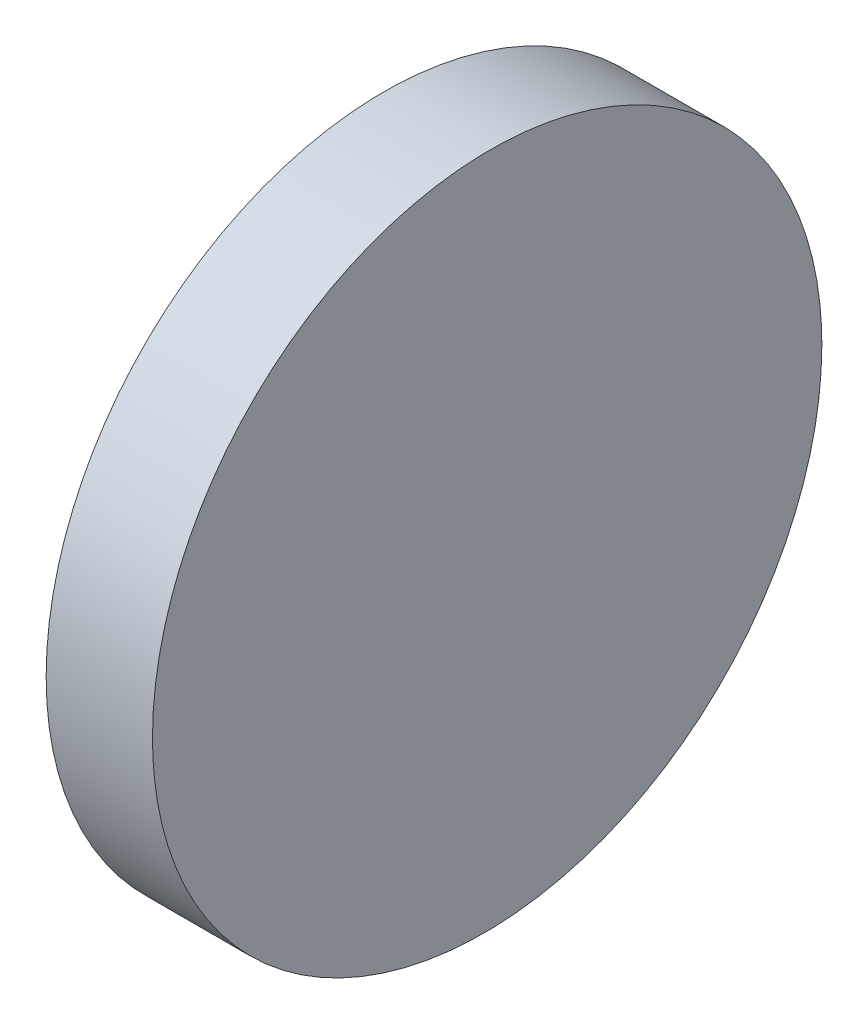
SolidWorks part; units mm, degrees
ref_plane "前视基准面" through (0, 0, 0) normal (0, 0, 1) x (1, 0, 0)
ref_plane "上视基准面" through (0, 0, 0) normal (0, 1, 0) x (1, 0, 0)
ref_plane "右视基准面" through (0, 0, 0) normal (1, 0, 0) x (0, 0, -1)
sketch "草图1" plane through (0, 0, 0) normal (0, 1, 0) x (1, 0, 0)
  line L0 (-12.1202, 0) -> (19.0875, 0) construction
  line L1 (0, 25.4) -> (0, -25.4)
  line L2 (0, -25.4) -> (8, -25.4)
  line L3 (8, -25.4) -> (7.5567, 25.4)
  line L4 (0, 25.4) -> (7.5567, 25.4)
  point P5 (0, 0)
  dimension "D1" = 8
  dimension "D2" = 50.8
  dimension "D3" = 0.5
extrude "凸台-拉伸1" add sketch "草图1" along normal blind 50.8
sketch "草图5" plane through (0, 0, 0) normal (-1, 0, 0) x (0, 0, 1)
  line L0 (0, 0) -> (0, 50.8) construction
  line L1 (-25.4, 50.8) -> (25.4, 50.8) construction
  line L2 (0, 50.8) -> (0.9302, 12.292) construction
  line L3 (-25.4, 25.4) -> (25.4, 25.4) construction
  line L4 (-25.4, 50.8) -> (-25.4, 0) construction
  line L5 (25.4, 50.8) -> (25.4, 0) construction
  line L6 (25.4, 25.4) -> (6.6453, 6.1075) construction
  line L11 (-25.4, 0) -> (25.4, 0)
  line L12 (25.4, 0) -> (25.4, 50.8)
  line L13 (25.4, 50.8) -> (-25.4, 50.8)
  line L14 (-25.4, 50.8) -> (-25.4, 0)
  line L15 (-25.4, 0) -> (25.4, 0)
  line L16 (25.4, 0) -> (25.4, 50.8)
  line L17 (25.4, 50.8) -> (-25.4, 50.8)
  line L18 (-25.4, 50.8) -> (-25.4, 0)
  circle A0 centre (0, 25.4) radius 25.4
  line M5 (-25.4, 0) -> (25.4, 0)
  line M6 (25.4, 0) -> (25.4, 50.8)
  line M7 (25.4, 50.8) -> (-25.4, 50.8)
  line M8 (-25.4, 50.8) -> (-25.4, 0)
  dimension "D1" = 50.8
  dimension "D2" = 0
extrude "切除-拉伸2" cut sketch "草图5" against normal blind 12.5 contours A0 L17 M8 | A0 L18 M5 | A0 L15 M6 | A0 L16 M7
